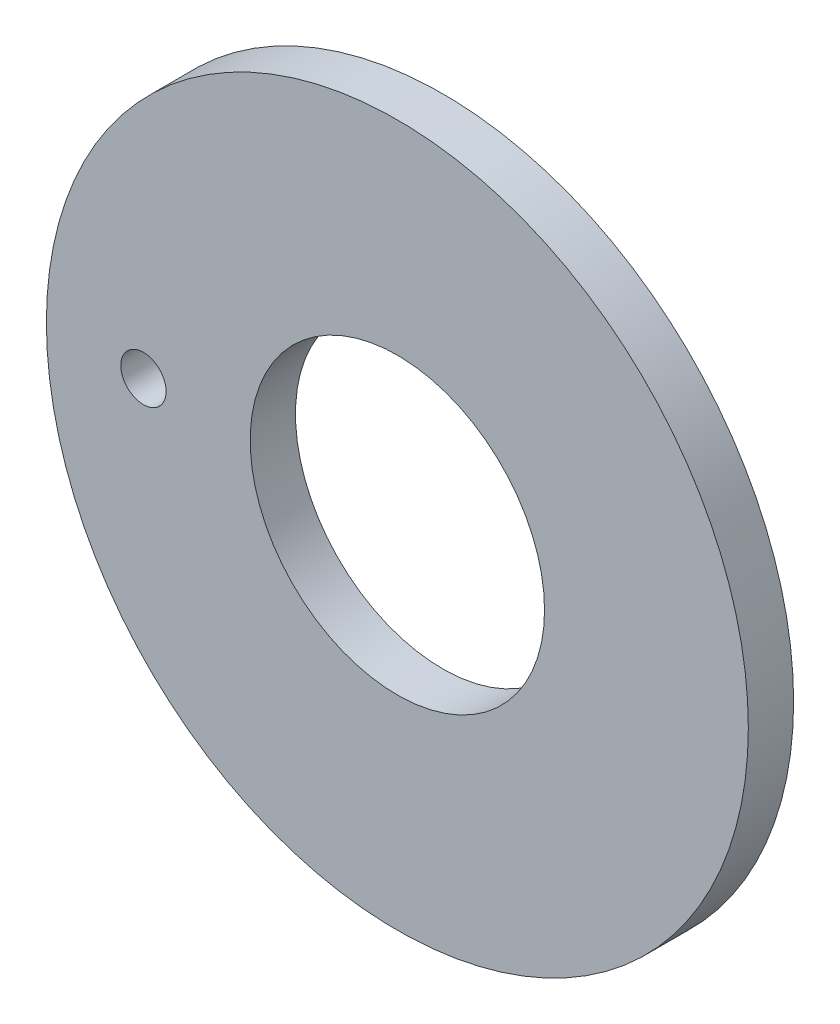
SolidWorks part; units mm, degrees
ref_plane "Front Plane" through (0, 0, 0) normal (0, 0, 1) x (1, 0, 0)
ref_plane "Top Plane" through (0, 0, 0) normal (0, 1, 0) x (1, 0, 0)
ref_plane "Right Plane" through (0, 0, 0) normal (1, 0, 0) x (0, 0, -1)
sketch "Sketch1" plane through (0, 0, 0) normal (0, 0, 1) x (1, 0, 0)
  line L0 (0, 0) -> (-74.9399, 0) construction
  circle A0 centre (0, 0) radius 49.2125
  circle A1 centre (-35.6018, 0) radius 3.175
  circle A2 centre (0, 0) radius 35.6018 construction
  circle A3 centre (0, 0) radius 20.6375
  dimension "D1" = 98.425
  dimension "D2" = 13.6107
  dimension "D3" = 6.35
  dimension "D4" = 41.275
extrude "Boss-Extrude1" add sketch "Sketch1" along normal blind 6.35
